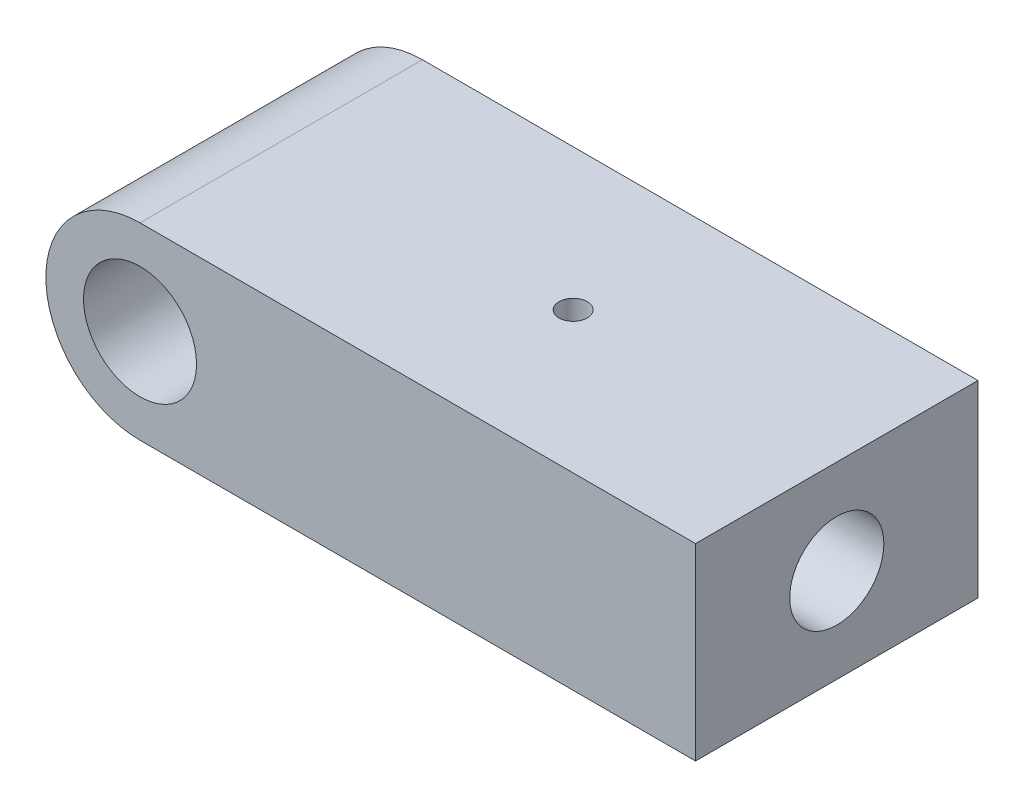
SolidWorks part; units mm, degrees
material "Alu 2017 (AU4G)"
ref_plane "Face" through (0, 0, 0) normal (0, 0, 1) x (1, 0, 0)
ref_plane "Dessus" through (0, 0, 0) normal (0, 1, 0) x (1, 0, 0)
ref_plane "Droite" through (0, 0, 0) normal (1, 0, 0) x (0, 0, -1)
sketch "Esquisse1" plane through (0, 0, 0) normal (0, 0, 1) x (1, 0, 0)
  line L0 (0, -10) -> (59, -10)
  line L2 (0, 10) -> (59, 10)
  line L3 (59, 10) -> (59, -10)
  arc A0 (0, 10) -> (0, -10) centre (0, 0) ccw
  circle A1 centre (0, 0) radius 6
  dimension "D3" = 12
  dimension "D1" = 20
  dimension "D2" = 59
extrude "Boss.-Extru.1" add sketch "Esquisse1" along normal mid plane 30
hole_wizard "Diamètre du perçage Ø10.0 (10)1" positions "Esquisse4" profile "Esquisse3" hole size "Ø10.0" standard "ISO"
sketch "Esquisse4" plane through (59, 0, 0) normal (1, 0, 0) x (0, 0, -1)
  point P0 (0, 0)
sketch "Esquisse3" plane through (59, 0, 0) normal (0, 1, 0) x (0, 0, -1)
  line L0 (0, 0) -> (0, 43.0043)
  line L1 (0, 43.0043) -> (5, 40)
  line L2 (5, 40) -> (5, 0)
  line L5 (5, 0) -> (0, 0)
  line L10 (0, 43.0043) -> (-5, 40) construction
  line L11 (0, -6.35) -> (0, 107.95) construction
  dimension "Diamètre du perçage" = 10
  dimension "Profondeur du perçage" = 40
  dimension "Angle de pointe" = 118
hole_wizard "Diamètre du perçage Ø3.0 (3)1" positions "Esquisse6" profile "Esquisse5" hole size "Ø3.0" standard "ISO"
sketch "Esquisse6" plane through (0, 10, 0) normal (0, 1, 0) x (1, 0, 0)
  line L0 (59, -15) -> (59, 15) construction
  point P0 (31, 0)
  dimension "D1" = 28
sketch "Esquisse5" plane through (31, 10, 0) normal (1, 0, 0) x (0, 0, 1)
  line L0 (0, 0) -> (0, 10.9013)
  line L1 (0, 10.9013) -> (1.5, 10)
  line L2 (1.5, 10) -> (1.5, 0)
  line L5 (1.5, 0) -> (0, 0)
  line L10 (0, 10.9013) -> (-1.5, 10) construction
  line L11 (0, -6.35) -> (0, 107.95) construction
  dimension "Diamètre du perçage" = 3
  dimension "Profondeur du perçage" = 10
  dimension "Angle de pointe" = 118
hole_wizard "Trou taraudé M41" positions "Esquisse8" profile "Esquisse7" tap size "M4" standard "ISO"
sketch "Esquisse8" plane through (0, -10, 0) normal (0, -1, 0) x (-1, 0, 0)
  line L0 (-59, -15) -> (-59, 15) construction
  point P0 (-40, 0)
  point P2 (-23, 0)
  dimension "D1" = 19
  dimension "D2" = 17
sketch "Esquisse7" plane through (40, -10, 0) normal (1, 0, 0) x (0, 0, -1)
  line L0 (0, 0) -> (0, 12.4914)
  line L1 (0, 12.4914) -> (1.65, 11.5)
  line L2 (1.65, 11.5) -> (1.65, 0)
  line L5 (1.65, 0) -> (0, 0)
  line L10 (0, 12.4914) -> (-1.65, 11.5) construction
  line L11 (0, -6.35) -> (0, 107.95) construction
  dimension "Diamètre du trou pour taraudage" = 3.3
  dimension "Profondeur du trou pour taraudage" = 11.5
  dimension "Angle de pointe" = 118
cosmetic thread "Filetage de perçage1" parameters "D1"=5.2801, "D2"=4
cosmetic thread "Filetage de perçage2" parameters "D1"=5.2801, "D2"=4
